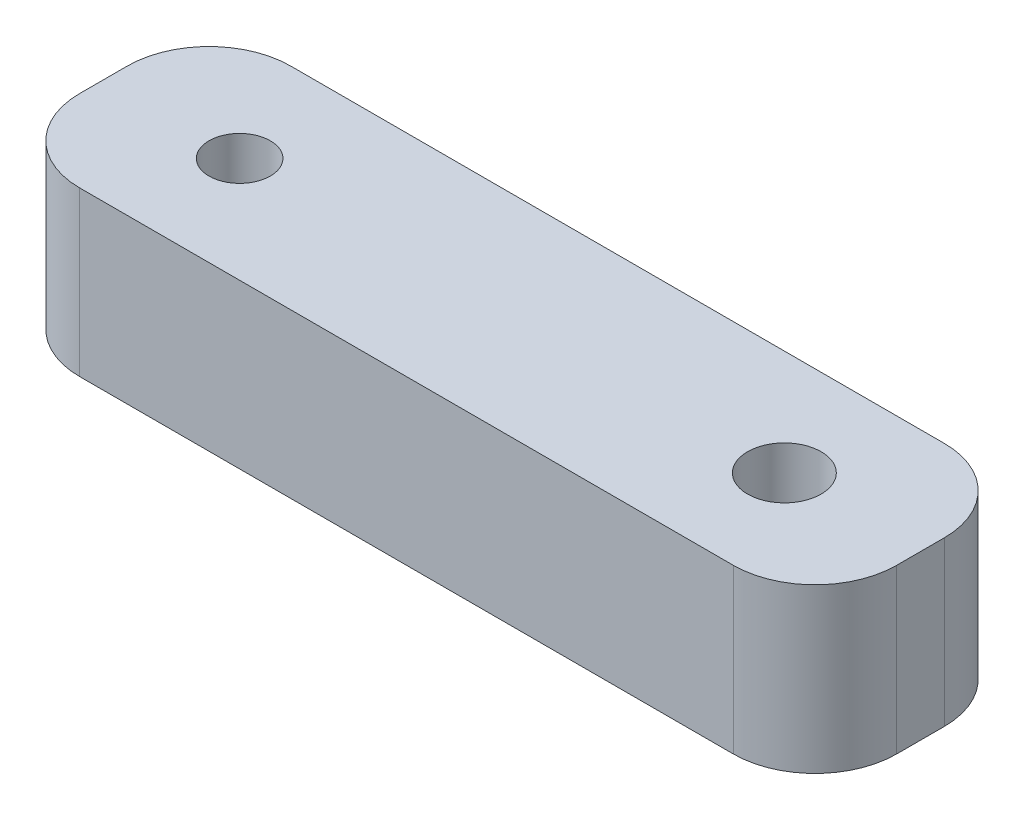
SolidWorks part; units mm, degrees
ref_plane "Front Plane" through (0, 0, 0) normal (0, 0, 1) x (1, 0, 0)
ref_plane "Top Plane" through (0, 0, 0) normal (0, 1, 0) x (1, 0, 0)
ref_plane "Right Plane" through (0, 0, 0) normal (1, 0, 0) x (0, 0, -1)
sketch "Sketch1" plane through (0, 0, 0) normal (0, 1, 0) x (1, 0, 0)
  line L1 (-12, 3.875) -> (12, 3.875)
  line L2 (-15, 0.875) -> (-15, -0.875)
  line L3 (-12, -3.875) -> (12, -3.875)
  line L4 (15, 0.875) -> (15, -0.875)
  line L5 (-15, 3.875) -> (15, -3.875) construction
  line L6 (-15, -3.875) -> (15, 3.875) construction
  arc A0 (-15, -0.875) -> (-12, -3.875) centre (-12, -0.875) ccw
  arc A1 (12, -3.875) -> (15, -0.875) centre (12, -0.875) ccw
  arc A2 (12, 3.875) -> (15, 0.875) centre (12, 0.875) cw
  arc A3 (-12, 3.875) -> (-15, 0.875) centre (-12, 0.875) ccw
  point P0 (0, 0)
  dimension "D3" = 3
  dimension "D1" = 24
  dimension "D2" = 7.75
extrude "Boss-Extrude1" add sketch "Sketch1" along normal blind 6
sketch "Sketch2" plane through (0, 6, 0) normal (0, 1, 0) x (1, 0, 0)
  line L0 (-10, 0) -> (-15, 0) construction
  line L1 (-15, 0.875) -> (-15, -0.875) construction
  line L2 (0, 3.875) -> (0, -3.875) construction
  line L3 (12, 3.875) -> (-12, 3.875) construction
  line L4 (-12, -3.875) -> (12, -3.875) construction
  line L5 (10, 0) -> (15, 0) construction
  circle A0 centre (-10, 0) radius 1.125
  circle A1 centre (10, 0) radius 1.35
  dimension "D1" = 2.25
  dimension "D2" = 2.7
  dimension "D3" = 5
extrude "Cut-Extrude1" cut sketch "Sketch2" against normal through all
